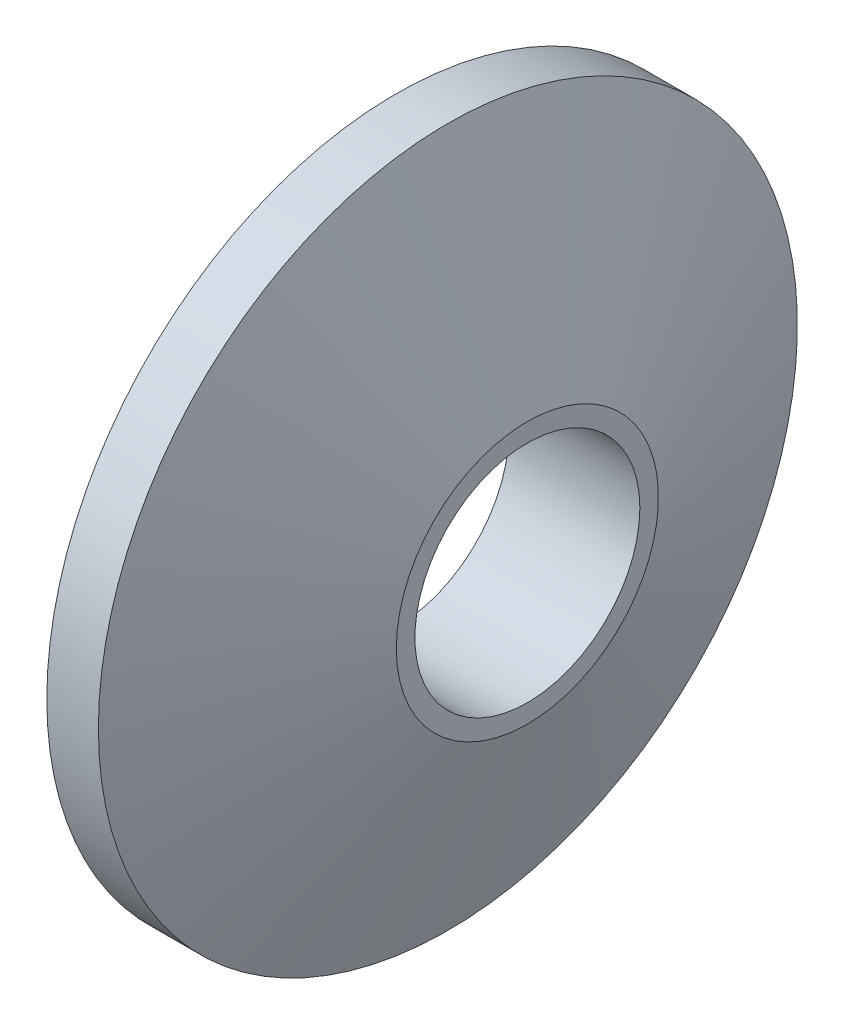
SolidWorks part; units mm, degrees
ref_plane "Front Plane" through (0, 0, 0) normal (0, 0, 1) x (1, 0, 0)
ref_plane "Top Plane" through (0, 0, 0) normal (0, 1, 0) x (1, 0, 0)
ref_plane "Right Plane" through (0, 0, 0) normal (1, 0, 0) x (0, 0, -1)
sketch "Sketch1" plane through (0, 0, 0) normal (0, 0, 1) x (1, 0, 0)
  line L0 (-13.2766, 0) -> (17.0213, 0) construction
  line L3 (0, 0) -> (0, 8)
  line L7 (3, 3) -> (3, 0)
  line L8 (3, 0) -> (0, 0)
  line L9 (0, 8) -> (1.1801, 8)
  line L10 (1.1801, 8) -> (3, 3)
  dimension "D1" = 8
  dimension "D2" = 3
  dimension "D3" = 5
  dimension "D4" = 160
revolve "Revolve1" add sketch "Sketch1" angle 360 about L0
sketch "Sketch2" plane through (3, 0, 0) normal (1, 0, 0) x (0, 0, -1)
  line L2 (-0.25, 2.2361) -> (-0.25, 2.4861)
  line L3 (-0.25, 2.4861) -> (0.25, 2.4861)
  line L4 (0.25, 2.2361) -> (0.25, 2.4861)
  line L5 (0, 2.25) -> (0.25, 2.4861) construction
  line L6 (-0.25, 2.4861) -> (0, 2.25) construction
  arc A0 (-0.25, 2.2361) -> (0.25, 2.2361) centre (0, 0) ccw
  point P3 (0, 2.25)
  dimension "D1" = 4.5
  dimension "D2" = 0.5
  dimension "D3" = 0.25
  dimension "D4" = 0.0139
extrude "Cut-Extrude1" [suppressed] cut sketch "Sketch2" against normal through all
sketch "Sketch5" plane through (3, 0, 0) normal (1, 0, 0) x (0, 0, -1)
  circle A0 centre (0, 0) radius 2.575
  dimension "D1" = 5.15
extrude "Cut-Extrude3" cut sketch "Sketch5" against normal through all
sketch "Sketch4" plane through (3, 0, 0) normal (1, 0, 0) x (0, 0, -1)
  circle A0 centre (0, 0) radius 3
  dimension "D1" = 6
extrude "Cut-Extrude2" [suppressed] cut sketch "Sketch4" against normal blind 0.5
